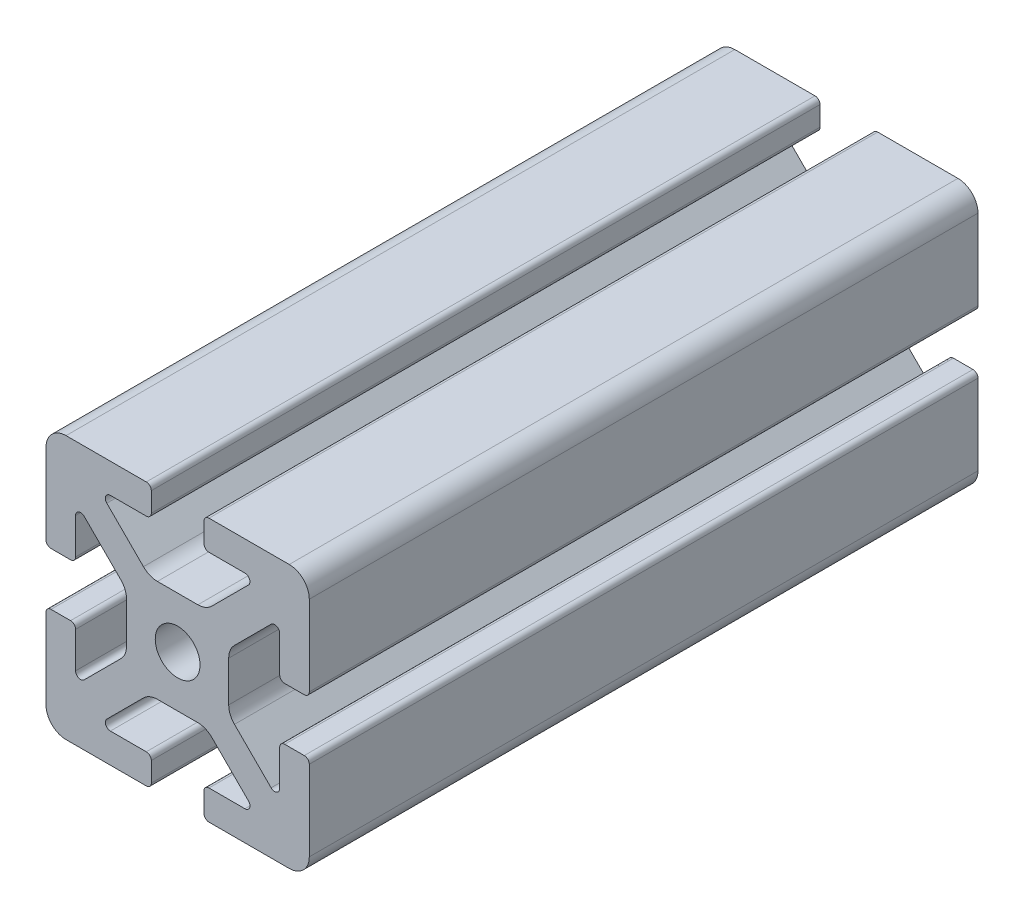
SolidWorks part; units mm, degrees
ref_plane "Front Plane" through (0, 0, 0) normal (0, 0, 1) x (1, 0, 0)
ref_plane "Top Plane" through (0, 0, 0) normal (0, 1, 0) x (1, 0, 0)
ref_plane "Right Plane" through (0, 0, 0) normal (1, 0, 0) x (0, 0, -1)
sketch "Sketch1" plane through (0, 0, 0) normal (0, 0, 1) x (1, 0, 0)
  line L2 (-20, 16.952) -> (-20, 4.7625)
  line L3 (-16.952, 20) -> (-4.7625, 20)
  line L4 (-4.0005, 19.238) -> (-4.0005, 16.2662)
  line L5 (-4.7625, 15.5042) -> (-10.2235, 15.5042)
  line L6 (-10.7623, 14.2034) -> (-5.194, 8.6351)
  line L7 (-14.2034, 10.7623) -> (-8.6351, 5.194)
  line L8 (-15.5042, 10.2235) -> (-15.5042, 4.7625)
  line L9 (-16.2662, 4.0005) -> (-19.238, 4.0005)
  line L11 (-3.0746, 7.7572) -> (3.0746, 7.7572)
  line L12 (-7.7572, 3.0746) -> (-7.7572, -3.0746)
  line L13 (16.2662, 4.0005) -> (19.238, 4.0005)
  line L14 (15.5042, 10.2235) -> (15.5042, 4.7625)
  line L15 (20, 16.952) -> (20, 4.7625)
  line L16 (16.952, 20) -> (4.7625, 20)
  line L17 (4.0005, 19.238) -> (4.0005, 16.2662)
  line L18 (4.7625, 15.5042) -> (10.2235, 15.5042)
  line L19 (7.7572, 3.0746) -> (7.7572, -3.0746)
  line L20 (10.7623, 14.2034) -> (5.194, 8.6351)
  line L21 (14.2034, 10.7623) -> (8.6351, 5.194)
  line L22 (-16.2662, -4.0005) -> (-19.238, -4.0005)
  line L23 (-15.5042, -10.2235) -> (-15.5042, -4.7625)
  line L24 (-14.2034, -10.7623) -> (-8.6351, -5.194)
  line L25 (-10.7623, -14.2034) -> (-5.194, -8.6351)
  line L26 (-4.7625, -15.5042) -> (-10.2235, -15.5042)
  line L27 (-4.0005, -19.238) -> (-4.0005, -16.2662)
  line L28 (-16.952, -20) -> (-4.7625, -20)
  line L29 (-20, -16.952) -> (-20, -4.7625)
  line L30 (20, -16.952) -> (20, -4.7625)
  line L31 (16.952, -20) -> (4.7625, -20)
  line L32 (4.0005, -19.238) -> (4.0005, -16.2662)
  line L33 (4.7625, -15.5042) -> (10.2235, -15.5042)
  line L34 (10.7623, -14.2034) -> (5.194, -8.6351)
  line L35 (14.2034, -10.7623) -> (8.6351, -5.194)
  line L36 (15.5042, -10.2235) -> (15.5042, -4.7625)
  line L37 (16.2662, -4.0005) -> (19.238, -4.0005)
  line L38 (-3.0746, -7.7572) -> (3.0746, -7.7572)
  circle A0 centre (0, 0) radius 3.4036
  arc A1 (-20, 16.952) -> (-16.952, 20) centre (-16.952, 16.952) cw
  arc A2 (-14.2034, 10.7623) -> (-15.5042, 10.2235) centre (-14.7422, 10.2235) ccw
  arc A3 (-10.2235, 15.5042) -> (-10.7623, 14.2034) centre (-10.2235, 14.7422) ccw
  arc A4 (-4.7625, 20) -> (-4.0005, 19.238) centre (-4.7625, 19.238) cw
  arc A5 (-20, 4.7625) -> (-19.238, 4.0005) centre (-19.238, 4.7625) ccw
  arc A6 (-15.5042, 4.7625) -> (-16.2662, 4.0005) centre (-16.2662, 4.7625) cw
  arc A7 (-4.0005, 16.2662) -> (-4.7625, 15.5042) centre (-4.7625, 16.2662) cw
  arc A8 (-3.0746, 7.7572) -> (-5.194, 8.6351) centre (-3.0746, 10.7544) cw
  arc A9 (-7.7572, 3.0746) -> (-8.6351, 5.194) centre (-10.7544, 3.0746) ccw
  arc A10 (15.5042, 4.7625) -> (16.2662, 4.0005) centre (16.2662, 4.7625) ccw
  arc A11 (20, 4.7625) -> (19.238, 4.0005) centre (19.238, 4.7625) cw
  arc A12 (20, 16.952) -> (16.952, 20) centre (16.952, 16.952) ccw
  arc A13 (4.7625, 20) -> (4.0005, 19.238) centre (4.7625, 19.238) ccw
  arc A14 (4.0005, 16.2662) -> (4.7625, 15.5042) centre (4.7625, 16.2662) ccw
  arc A15 (3.0746, 7.7572) -> (5.194, 8.6351) centre (3.0746, 10.7544) ccw
  arc A16 (7.7572, 3.0746) -> (8.6351, 5.194) centre (10.7544, 3.0746) cw
  arc A17 (14.2034, 10.7623) -> (15.5042, 10.2235) centre (14.7422, 10.2235) cw
  arc A18 (10.2235, 15.5042) -> (10.7623, 14.2034) centre (10.2235, 14.7422) cw
  arc A19 (-7.7572, -3.0746) -> (-8.6351, -5.194) centre (-10.7544, -3.0746) cw
  arc A20 (-3.0746, -7.7572) -> (-5.194, -8.6351) centre (-3.0746, -10.7544) ccw
  arc A21 (-4.0005, -16.2662) -> (-4.7625, -15.5042) centre (-4.7625, -16.2662) ccw
  arc A22 (-15.5042, -4.7625) -> (-16.2662, -4.0005) centre (-16.2662, -4.7625) ccw
  arc A23 (-20, -4.7625) -> (-19.238, -4.0005) centre (-19.238, -4.7625) cw
  arc A24 (-4.7625, -20) -> (-4.0005, -19.238) centre (-4.7625, -19.238) ccw
  arc A25 (-10.2235, -15.5042) -> (-10.7623, -14.2034) centre (-10.2235, -14.7422) cw
  arc A26 (-14.2034, -10.7623) -> (-15.5042, -10.2235) centre (-14.7422, -10.2235) cw
  arc A27 (-20, -16.952) -> (-16.952, -20) centre (-16.952, -16.952) ccw
  arc A28 (20, -16.952) -> (16.952, -20) centre (16.952, -16.952) cw
  arc A29 (14.2034, -10.7623) -> (15.5042, -10.2235) centre (14.7422, -10.2235) ccw
  arc A30 (10.2235, -15.5042) -> (10.7623, -14.2034) centre (10.2235, -14.7422) ccw
  arc A31 (4.7625, -20) -> (4.0005, -19.238) centre (4.7625, -19.238) cw
  arc A32 (20, -4.7625) -> (19.238, -4.0005) centre (19.238, -4.7625) ccw
  arc A33 (15.5042, -4.7625) -> (16.2662, -4.0005) centre (16.2662, -4.7625) cw
  arc A34 (4.0005, -16.2662) -> (4.7625, -15.5042) centre (4.7625, -16.2662) cw
  arc A35 (3.0746, -7.7572) -> (5.194, -8.6351) centre (3.0746, -10.7544) cw
  arc A36 (7.7572, -3.0746) -> (8.6351, -5.194) centre (10.7544, -3.0746) ccw
extrude "Boss-Extrude1" add sketch "Sketch1" along normal mid plane 760
sketch "Sketch2" plane through (0, 0, 0) normal (1, 0, 0) x (0, 0, -1)
  line L0 (-380, -20) -> (380, -20) construction
  line L1 (380, 20) -> (1, 20)
  line L2 (380, 20) -> (380, -20)
  line L3 (380, -20) -> (1, -20)
  line L4 (1, 20) -> (1, -20)
extrude "Cut-Extrude1" cut sketch "Sketch2" against normal blind 71 and the other way blind 65
sketch "Sketch4" plane through (0, 0, 0) normal (1, 0, 0) x (0, 0, -1)
  line L1 (1, 20) -> (-278.4, 20)
  line L2 (1, 20) -> (1, -35.5377)
  line L3 (1, -35.5377) -> (-278.4, -35.5377)
  line L4 (-278.4, 20) -> (-278.4, -35.5377)
extrude "Cut-Extrude2" cut sketch "Sketch4" against normal blind 30 and the other way blind 30
